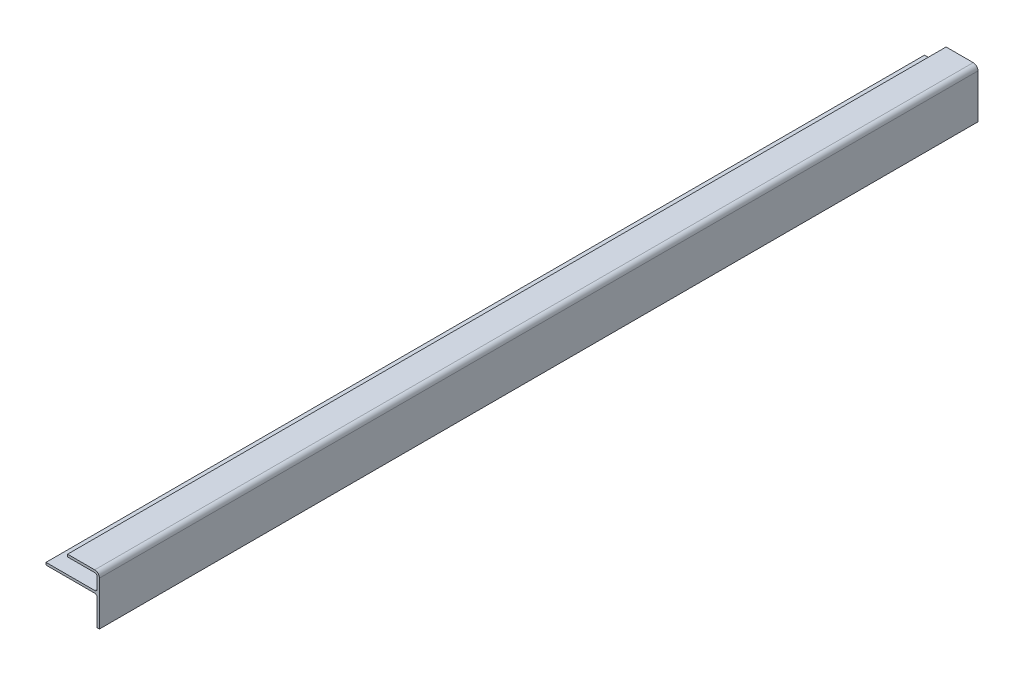
SolidWorks part; units mm, degrees
material "Pure Lead"
ref_plane "Front Plane" through (0, 0, 0) normal (0, 0, 1) x (1, 0, 0)
ref_plane "Top Plane" through (0, 0, 0) normal (0, 1, 0) x (1, 0, 0)
ref_plane "Right Plane" through (0, 0, 0) normal (1, 0, 0) x (0, 0, -1)
sketch "Sketch1" plane through (0, 0, 0) normal (0, 0, 1) x (1, 0, 0)
  line L0 (1219.2, 19.05) -> (1219.2, 36.5125)
  line L1 (1217.6125, 38.1) -> (1185.2275, 38.1)
  line L2 (1220.7875, 48.387) -> (1220.7875, 19.05)
  line L3 (1217.6125, 51.562) -> (1199.5785, 51.562)
  line L4 (1199.5785, 49.9745) -> (1217.6125, 49.9745)
  line L5 (1219.2, 48.387) -> (1219.2, 41.275)
  line L6 (1185.2275, 39.6875) -> (1217.6125, 39.6875)
  line L7 (1199.5785, 51.562) -> (1199.5785, 49.9745)
  line L9 (1185.2275, 38.1) -> (1185.2275, 39.6875)
  line L10 (1219.2, 19.05) -> (1220.7875, 19.05)
  arc A0 (1219.2, 36.5125) -> (1217.6125, 38.1) centre (1217.6125, 36.5125) ccw
  arc A1 (1220.7875, 48.387) -> (1217.6125, 51.562) centre (1217.6125, 48.387) ccw
  arc A2 (1219.2, 48.387) -> (1217.6125, 49.9745) centre (1217.6125, 48.387) ccw
  arc A3 (1217.6125, 39.6875) -> (1219.2, 41.275) centre (1217.6125, 41.275) ccw
extrude "Extrude1" add sketch "Sketch1" along normal mid plane 584.2
